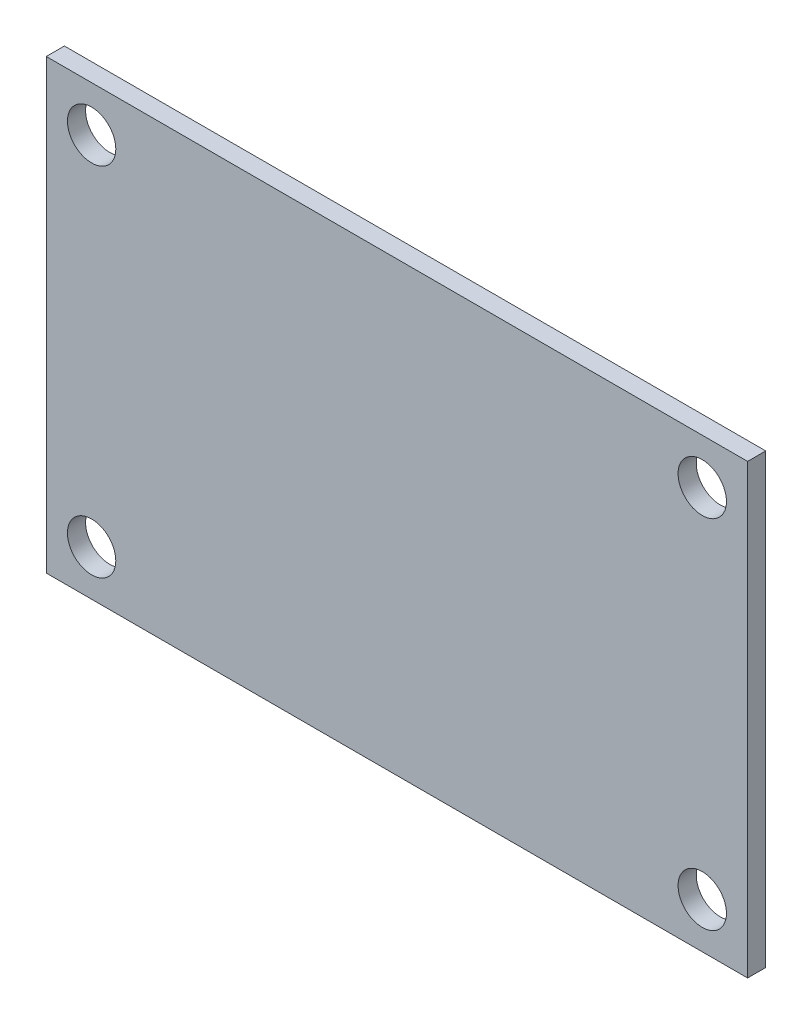
SolidWorks part; units mm, degrees
ref_plane "Plan de face" through (0, 0, 0) normal (0, 0, 1) x (1, 0, 0)
ref_plane "Plan de dessus" through (0, 0, 0) normal (0, 1, 0) x (1, 0, 0)
ref_plane "Plan de droite" through (0, 0, 0) normal (1, 0, 0) x (0, 0, -1)
sketch "Main-Sketch" plane through (0, 0, 0) normal (0, 0, 1) x (1, 0, 0)
  line L1 (0, 0) -> (58, 0)
  line L2 (0, 0) -> (0, 37)
  line L3 (0, 37) -> (58, 37)
  line L4 (58, 0) -> (58, 37)
  circle A0 centre (3.75, 33.25) radius 2
  circle A1 centre (54.25, 33.25) radius 2
  circle A2 centre (54.25, 3.75) radius 2
  circle A3 centre (3.75, 3.75) radius 2
  point P13 (0, 0)
  point P14 (0, 0)
  point P15 (0, 0)
  point P16 (3.75, 6.0231)
  point P17 (0, 0)
  point P18 (0, 0)
  point P19 (54.25, 33.25)
  dimension "D3" = 4
  dimension "D1" = 58
  dimension "D2" = 37
  dimension "D4" = 3.75
  dimension "D5" = 3.75
  dimension "D6" = 3.75
  dimension "D7" = 3.75
  dimension "D8" = 50.5
  dimension "D9" = 29.5
extrude "Main" add sketch "Main-Sketch" along normal blind 1.5
